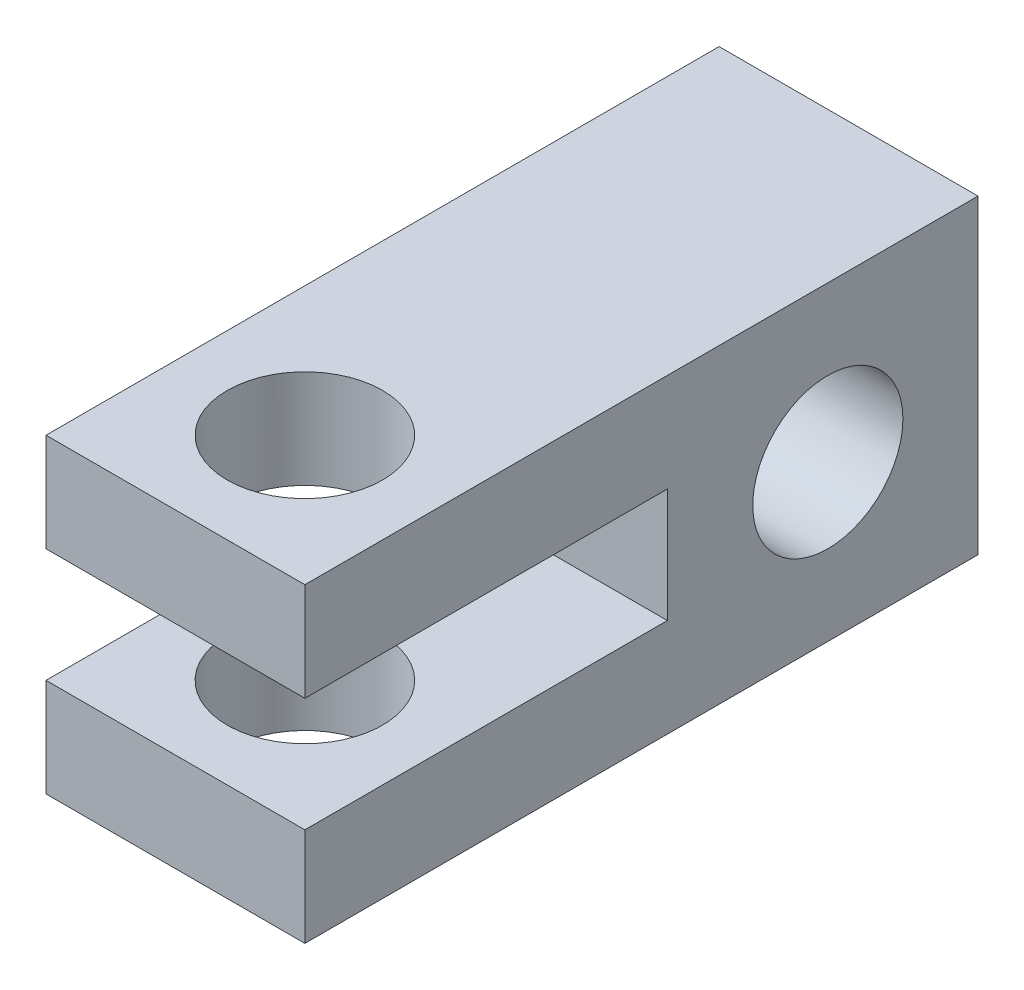
SolidWorks part; units mm, degrees
ref_plane "Front Plane" through (0, 0, 0) normal (0, 0, 1) x (1, 0, 0)
ref_plane "Top Plane" through (0, 0, 0) normal (0, 1, 0) x (1, 0, 0)
ref_plane "Right Plane" through (0, 0, 0) normal (1, 0, 0) x (0, 0, -1)
sketch "Sketch1" plane through (0, 0, 0) normal (0, 1, 0) x (1, 0, 0)
  line L1 (0, 0) -> (6.35, 0)
  line L2 (0, 0) -> (0, 16.51)
  line L3 (0, 16.51) -> (6.35, 16.51)
  line L4 (6.35, 0) -> (6.35, 16.51)
  circle A0 centre (3.175, 3.175) radius 1.905
  point P7 (0, 0)
  point P8 (3.175, 0)
  dimension "D3" = 3.81
  dimension "D1" = 6.35
  dimension "D2" = 16.51
  dimension "D4" = 3.175
extrude "Boss-Extrude1" add sketch "Sketch1" along normal blind 7.62
sketch "Sketch2" plane through (0, 0, 0) normal (0, 0, 1) x (1, 0, 0)
  line L0 (0, 7.62) -> (0, 0) construction
  line L1 (0, 2.413) -> (6.35, 2.413)
  line L2 (0, 2.413) -> (0, 5.207)
  line L3 (0, 5.207) -> (6.35, 5.207)
  line L4 (6.35, 2.413) -> (6.35, 5.207)
  line L5 (6.35, 7.62) -> (6.35, 0) construction
  point P8 (0, 3.81)
  point P9 (0, 3.81)
  dimension "D1" = 2.794
extrude "Cut-Extrude1" cut sketch "Sketch2" against normal blind 8.89 and the other way through all
sketch "Sketch4" plane through (6.35, 0, 0) normal (1, 0, 0) x (0, 0, -1)
  line L0 (8.89, 2.413) -> (8.89, 5.207) construction
  line L1 (16.51, 7.62) -> (16.51, 0) construction
  circle A0 centre (12.827, 3.81) radius 1.8415
  point P4 (8.89, 3.81)
  dimension "D1" = 3.683
  dimension "D2" = 3.683
extrude "Cut-Extrude2" cut sketch "Sketch4" against normal through all
